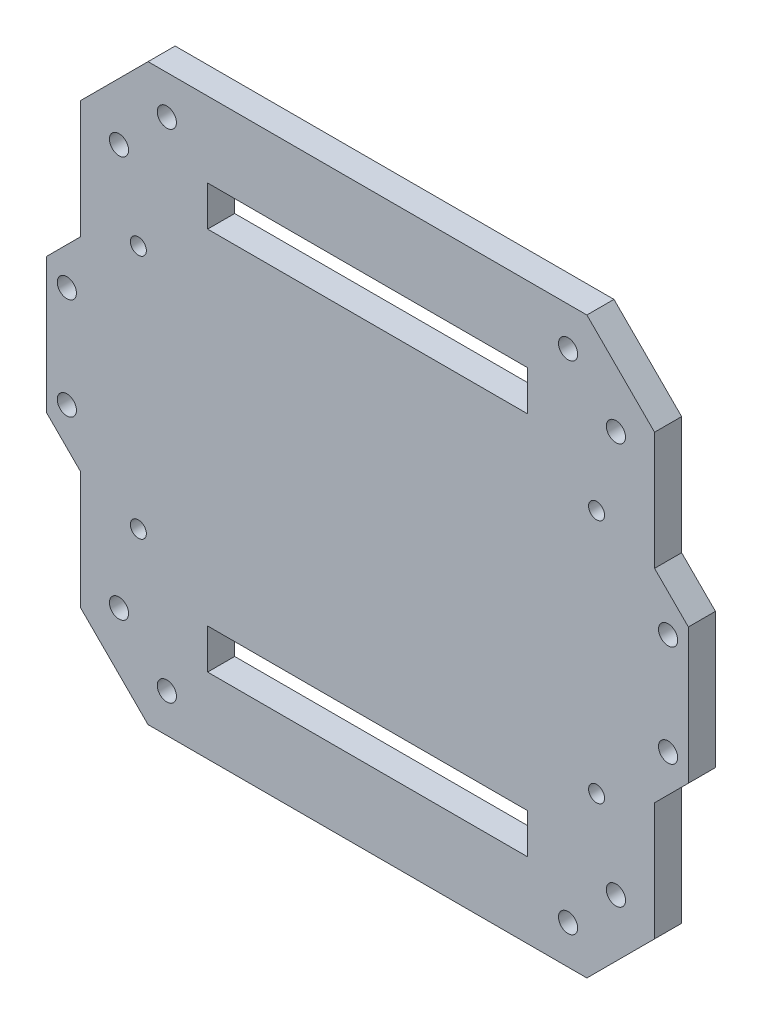
SolidWorks part; units mm, degrees
material "PETG CF"
ref_plane "Front Plane" through (0, 0, 0) normal (1, 0, 0) x (0, 1, 0)
ref_plane "Top Plane" through (0, 0, 0) normal (0, 0, 1) x (0, 1, 0)
ref_plane "Right Plane" through (0, 0, 0) normal (0, 1, 0) x (-1, 0, 0)
sketch "Sketch1" plane through (0, 0, 0) normal (0, 0, 1) x (0, 1, 0)
  line L5 (-41.1815, 53.8815) -> (-19.05, 53.8815)
  line L8 (53.8815, -53.8815) -> (19.05, -53.8815) construction
  line L17 (53.8815, -53.8815) -> (53.8815, 53.8815) construction
  line L18 (53.8815, 53.8815) -> (19.05, 53.8815) construction
  line L19 (-53.8815, -53.8815) -> (-53.8815, 53.8815) construction
  line L26 (-53.8815, 53.8815) -> (53.8815, -53.8815) construction
  line L27 (53.8815, 53.8815) -> (-53.8815, -53.8815) construction
  line L28 (41.1815, 53.8815) -> (53.8815, 41.1815)
  line L29 (53.8815, 41.1815) -> (53.8815, -41.1815)
  line L30 (53.8815, -41.1815) -> (41.1815, -53.8815)
  line L31 (41.1815, -53.8815) -> (19.05, -53.8815)
  line L32 (-41.1815, -53.8815) -> (-53.8815, -41.1815)
  line L33 (-53.8815, -41.1815) -> (-53.8815, 41.1815)
  line L34 (-53.8815, 41.1815) -> (-41.1815, 53.8815)
  line L35 (-46.6335, -37.6533) -> (-37.6533, -46.6335) construction
  line L40 (-19.05, -53.8815) -> (-12.7, -60.2315)
  line L42 (0, 70.5188) -> (0, -69.6931) construction
  line L43 (-68.9622, 0) -> (75.9812, 0) construction
  line L44 (23, -43) -> (-23, -43) construction
  line L45 (23, -43) -> (23, 43) construction
  line L46 (23, 43) -> (-23, 43) construction
  line L47 (-23, -43) -> (-23, 43) construction
  line L48 (23, -43) -> (-23, 43) construction
  line L49 (23, 43) -> (-23, -43) construction
  line L50 (-39.75, 30) -> (-32.25, 30)
  line L51 (-39.75, 30) -> (-39.75, -30)
  line L52 (-39.75, -30) -> (-32.25, -30)
  line L53 (-32.25, 30) -> (-32.25, -30)
  line L54 (-12.7, -60.2315) -> (12.7, -60.2315)
  line L55 (12.7, -60.2315) -> (19.05, -53.8815)
  line L56 (-19.05, 53.8815) -> (-12.7, 60.2315)
  line L57 (12.7, 60.2315) -> (19.05, 53.8815)
  line L58 (-12.7, 60.2315) -> (12.7, 60.2315)
  line L59 (-19.05, 53.8815) -> (-53.8815, 53.8815) construction
  line L60 (19.05, 53.8815) -> (41.1815, 53.8815)
  line L61 (-19.05, -53.8815) -> (-53.8815, -53.8815) construction
  line L62 (-19.05, -53.8815) -> (-41.1815, -53.8815)
  line L63 (-9.525, -56.4215) -> (9.525, -56.4215) construction
  line L64 (-9.525, 56.4215) -> (9.525, 56.4215) construction
  line L65 (39.75, -30) -> (32.25, -30)
  line L66 (39.75, 30) -> (39.75, -30)
  line L67 (39.75, 30) -> (32.25, 30)
  line L68 (32.25, 30) -> (32.25, -30)
  circle A0 centre (-46.6335, -37.6533) radius 1.8
  circle A1 centre (-37.6533, -46.6335) radius 1.8
  circle A6 centre (46.6335, -37.6533) radius 1.8
  circle A7 centre (37.6533, -46.6335) radius 1.8
  circle A8 centre (-46.6335, 37.6533) radius 1.8
  circle A9 centre (-37.6533, 46.6335) radius 1.8
  circle A10 centre (37.6533, 46.6335) radius 1.8
  circle A11 centre (46.6335, 37.6533) radius 1.8
  circle A12 centre (-23, 43) radius 1.5
  circle A13 centre (23, 43) radius 1.5
  circle A14 centre (-23, -43) radius 1.5
  circle A15 centre (23, -43) radius 1.5
  circle A21 centre (9.525, -56.4215) radius 1.8
  circle A22 centre (-9.525, -56.4215) radius 1.8
  circle A23 centre (-9.525, 56.4215) radius 1.8
  circle A24 centre (9.525, 56.4215) radius 1.8
  point P0 (0, 0)
  point P5 (0, 0)
  point P8 (0, 0)
  point P15 (0, 0)
  point P31 (0, 0)
  point P33 (-32.25, 0)
  point P40 (-42.1434, -42.1434)
  point P58 (0, -60.2315)
  point P61 (0, -56.4215)
  dimension "D4" = 3.6
  dimension "D9" = 3
  dimension "D20" = 3.6
  dimension "D1" = 152.4
  dimension "D2" = 107.7631
  dimension "D5" = 12.7
  dimension "D6" = 12.7
  dimension "D8" = 45
  dimension "D11" = 7.62
  dimension "D3" = 46
  dimension "D7" = 86
  dimension "D12" = 7.5
  dimension "D13" = 60
  dimension "D14" = 32.25
  dimension "D15" = 38.1
  dimension "D16" = 6.35
  dimension "D17" = 6.35
  dimension "D18" = 6.35
  dimension "D10" = 19.05
  dimension "D19" = 3.81
extrude "Boss-Extrude1" add sketch "Sketch1" along normal blind 5.08
equation "\"Width\"= sqr ( ( \"Diagonal\" ^ 2 ) / 2 )"
equation "\"depth\"= 0.2in"
equation "\"D1@Boss-Extrude1\"=\"depth\""
equation "\"Standoff Radius (M3)\"= 3mm'Radius of the standoffs for the wings (M5 screws)"
equation "\"Corner Spacing\"= 25in"
equation "\"Diagonal\"= 6in'Diagonal measurements of the standoff"
equation "\"D1@Sketch1\"=\"Diagonal\""
equation "\"D4@Sketch1\" = \"Standoff Radius (M3)\" + \"Tolerance\""
equation "\"Wing Standoff Spacing\"= 0.5in"
equation "\"D6@Sketch1\"=\"Wing Standoff Spacing\""
equation "\"Distance away for the wing holes\"= .4in"
equation "\"Tolerance\"= 0.6mm"
equation "\"Power Supply Hole Radius\"= 2.7mm"
equation "\"D20@Sketch1\"= \"Standoff Radius (M3)\" + \"Tolerance\""
equation "\"Le\"=6"
